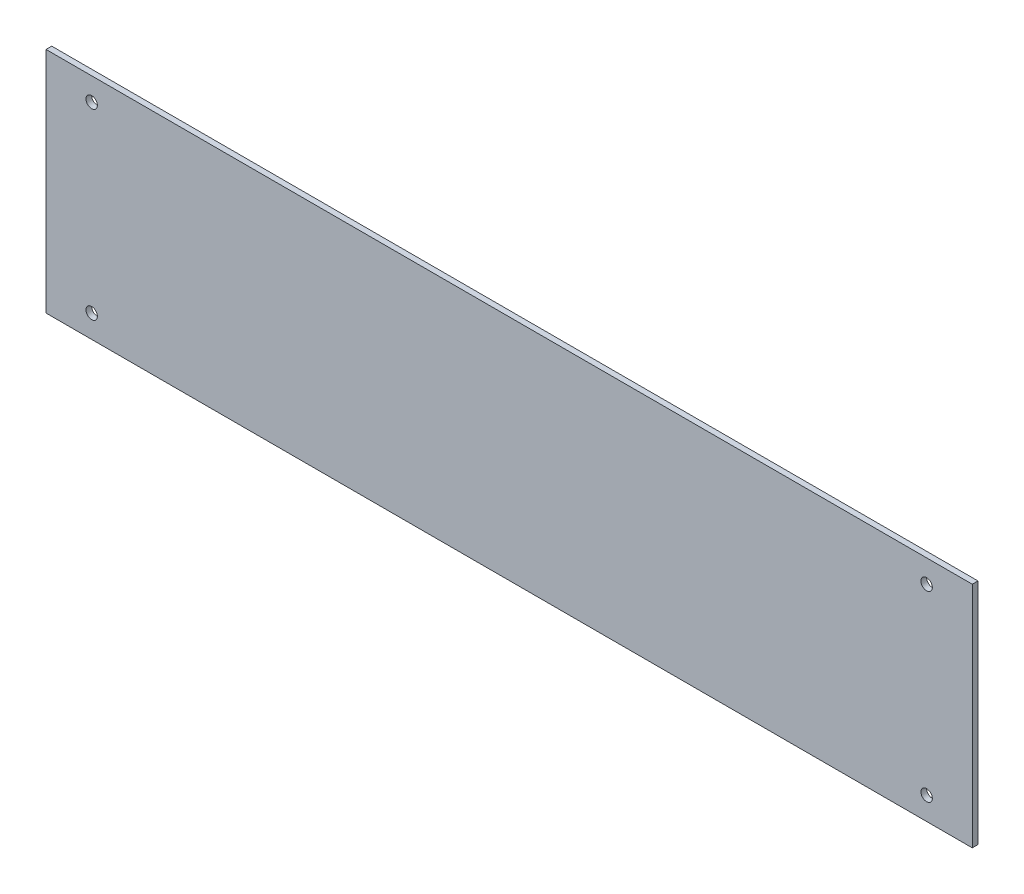
SolidWorks part; units mm, degrees
ref_plane "Front" through (0, 0, 0) normal (0, 0, 1) x (1, 0, 0)
ref_plane "Top" through (0, 0, 0) normal (0, 1, 0) x (1, 0, 0)
ref_plane "Right" through (0, 0, 0) normal (1, 0, 0) x (0, 0, -1)
sketch "Sketch1" plane through (0, 0, 0) normal (0, 0, 1) x (1, 0, 0)
  line L0 (-232.203, 63.5) -> (-232.203, -63.5) construction
  line L1 (-257.603, -63.5) -> (257.603, -63.5)
  line L2 (-257.603, -63.5) -> (-257.603, 63.5)
  line L3 (-257.603, 63.5) -> (257.603, 63.5)
  line L4 (257.603, -63.5) -> (257.603, 63.5)
  line L5 (-257.603, -63.5) -> (257.603, 63.5) construction
  line L6 (-257.603, 63.5) -> (257.603, -63.5) construction
  line L7 (232.203, 63.5) -> (232.203, -63.5) construction
  line L9 (232.203, -50.8) -> (-232.203, -50.8) construction
  line L10 (232.203, -50.8) -> (232.203, 50.8) construction
  line L11 (232.203, 50.8) -> (-232.203, 50.8) construction
  line L12 (-232.203, -50.8) -> (-232.203, 50.8) construction
  circle A0 centre (-232.203, 50.8) radius 3.175
  circle A1 centre (-232.203, -50.8) radius 3.175
  circle A2 centre (232.203, -50.8) radius 3.175
  circle A3 centre (232.203, 50.8) radius 3.175
  point P0 (0, 0)
  dimension "D7" = 6.35
  dimension "D1" = 515.206
  dimension "D2" = 127
  dimension "D3" = 12.7
  dimension "D4" = 25.4
  dimension "D5" = 12.7
  dimension "D6" = 25.4
extrude "Boss-Extrude1" add sketch "Sketch1" along normal blind 3.175
equation "\"D6@Sketch1\"=\"D4@Sketch1\""
